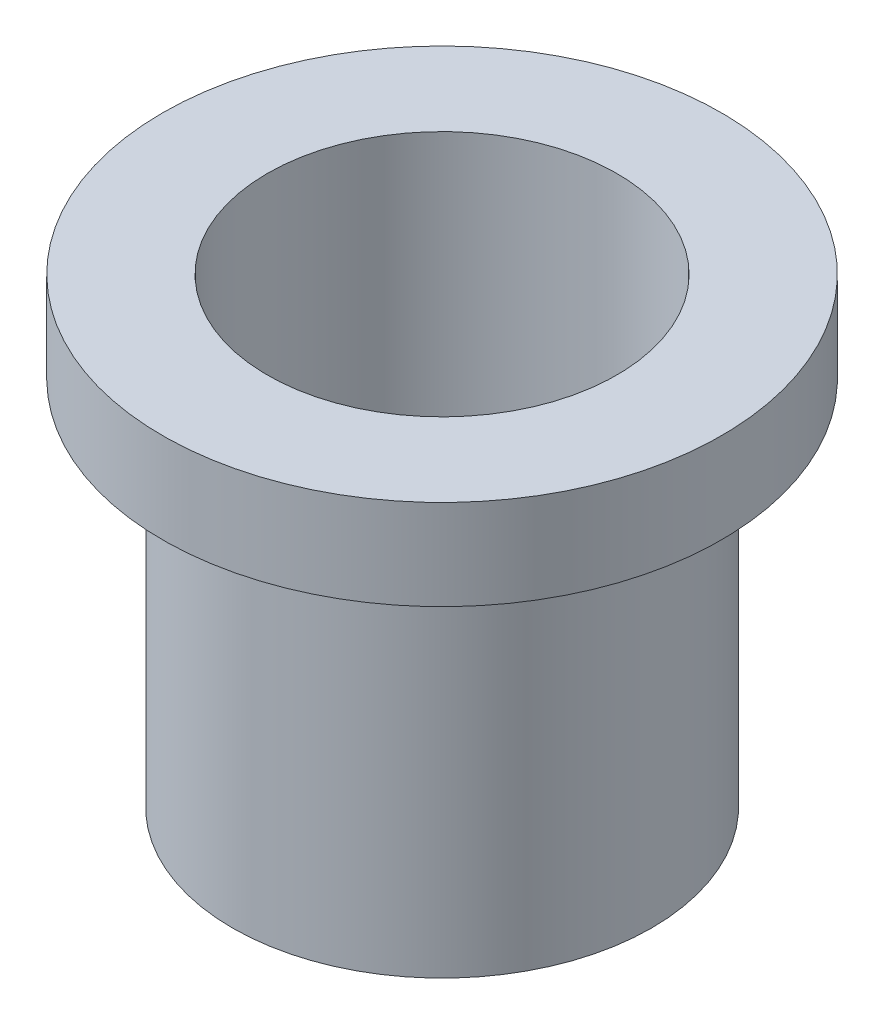
SolidWorks part; units mm, degrees
ref_plane "Front Plane" through (0, 0, 0) normal (0, 0, 1) x (1, 0, 0)
ref_plane "Top Plane" through (0, 0, 0) normal (0, 1, 0) x (1, 0, 0)
ref_plane "Right Plane" through (0, 0, 0) normal (1, 0, 0) x (0, 0, -1)
sketch "Sketch1" plane through (0, 0, 0) normal (0, 0, 1) x (1, 0, 0)
  line L0 (9.525, 0) -> (12.7, 0)
  line L1 (12.7, 0) -> (12.7, 4.1)
  line L2 (12.7, 4.1) -> (7.9375, 4.1)
  line L3 (7.9375, 4.1) -> (7.9375, -16.86)
  line L4 (7.9375, -16.86) -> (9.525, -16.86)
  line L5 (9.525, -16.86) -> (9.525, 0)
  line L7 (0, 35.7658) -> (0, -35.7658) construction
  dimension "D1" = 15.875
  dimension "D2" = 19.05
  dimension "D3" = 4.1
  dimension "D4" = 16.86
  dimension "D5" = 25.4
revolve "Revolve3" add sketch "Sketch1" angle 360 about L7
